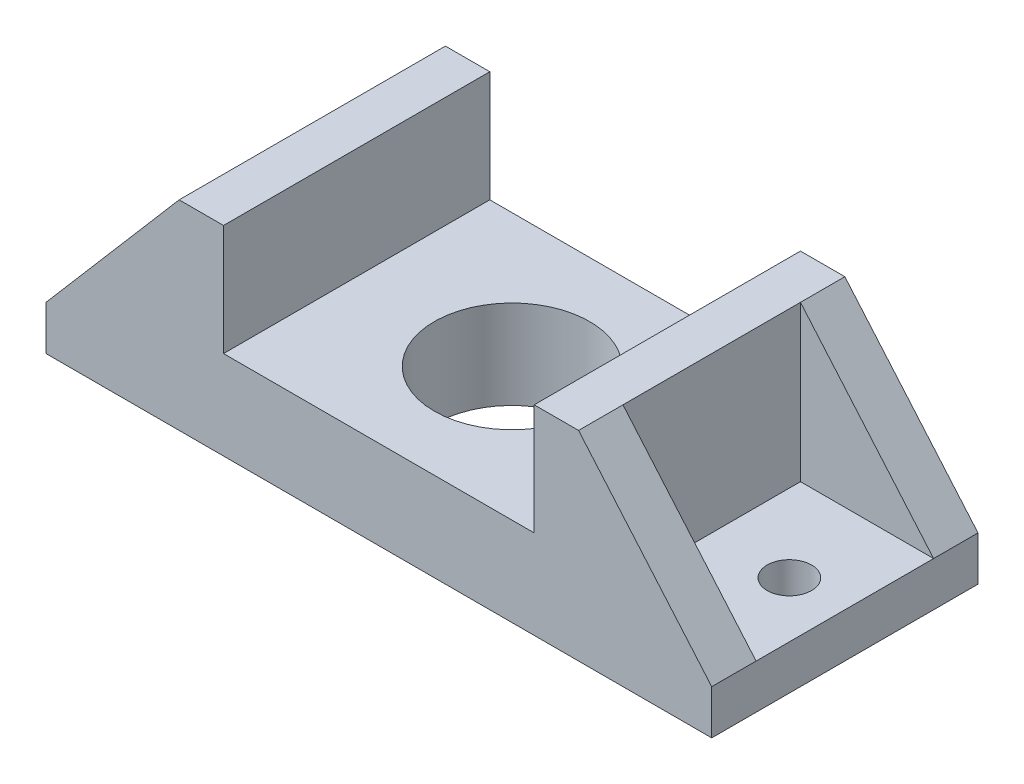
SolidWorks part; units mm, degrees
ref_plane "Ön Düzlem" through (0, 0, 0) normal (0, 0, 1) x (1, 0, 0)
ref_plane "Üst Düzlem" through (0, 0, 0) normal (0, 1, 0) x (1, 0, 0)
ref_plane "Sağ Düzlem" through (0, 0, 0) normal (1, 0, 0) x (0, 0, -1)
sketch "Çizim1" plane through (0, 0, 0) normal (0, 1, 0) x (1, 0, 0)
  line L1 (0, 0) -> (300, 0)
  line L2 (0, 0) -> (0, 120)
  line L3 (0, 120) -> (300, 120)
  line L4 (300, 0) -> (300, 120)
  dimension "D1" = 120
  dimension "D2" = 300
extrude "Yükseklik-Ekstrüzyon1" add sketch "Çizim1" along normal blind 20
sketch "Çizim2" plane through (0, 20, 0) normal (0, 1, 0) x (1, 0, 0)
  line L0 (300, 120) -> (0, 120) construction
  line L1 (60, 120) -> (80, 120)
  line L2 (60, 120) -> (60, 0)
  line L3 (60, 0) -> (80, 0)
  line L4 (80, 120) -> (80, 0)
  line L5 (0, 0) -> (300, 0) construction
  line L6 (0, 120) -> (0, 0) construction
  dimension "D1" = 20
  dimension "D2" = 60
extrude "Yükseklik-Ekstrüzyon2" add sketch "Çizim2" along normal blind 70
ref_plane "Düzlem1" through (150, 0, 0) normal (-1, 0, 0) x (0, 0, 1)
mirror "Aynalama1" about plane through (150, 0, 0) normal (-1, 0, 0) of "Yükseklik-Ekstrüzyon2"
sketch "Çizim3" plane through (0, 20, 0) normal (0, 1, 0) x (1, 0, 0)
  line L1 (80, 120) -> (220, 120)
  line L2 (80, 120) -> (80, 0)
  line L3 (80, 0) -> (220, 0)
  line L4 (220, 120) -> (220, 0)
extrude "Yükseklik-Ekstrüzyon3" add sketch "Çizim3" along normal blind 20
ref_plane "Düzlem2" through (0, 0, -60) normal (0, 0, 1) x (1, 0, 0)
sketch "Çizim4" plane through (0, 0, 0) normal (0, 0, 1) x (1, 0, 0)
  line L0 (0, 20) -> (60, 90)
  line L1 (60, 90) -> (60, 20)
  line L2 (60, 20) -> (0, 20)
extrude "Yükseklik-Ekstrüzyon4" add sketch "Çizim4" against normal blind 20
mirror "Aynalama2" about plane through (0, 0, -60) normal (0, 0, 1) of "Yükseklik-Ekstrüzyon4"
mirror "Aynalama3" about plane through (150, 0, 0) normal (-1, 0, 0) of "Aynalama2", "Yükseklik-Ekstrüzyon4"
sketch "Çizim5" plane through (0, 40, 0) normal (0, 1, 0) x (1, 0, 0)
  line L0 (0, 100) -> (0, 20) construction
  line L1 (220, 120) -> (80, 120) construction
  circle A0 centre (150, 60) radius 35
  dimension "D1" = 150
  dimension "D2" = 60
  dimension "D3" = 70
extrude "Kes-Ekstrüzyon1" cut sketch "Çizim5" against normal through all both and the other way through all
sketch "Çizim6" plane through (0, 20, 0) normal (0, 1, 0) x (1, 0, 0)
  line L0 (60, 120) -> (0, 120) construction
  line L1 (150, 120) -> (150, 54.9859) construction
  line L2 (220, 120) -> (80, 120) construction
  circle A0 centre (25, 60) radius 10
  circle A1 centre (150, 60) radius 35 construction
  circle A2 centre (275, 60) radius 10
  dimension "D1" = 20
  dimension "D2" = 125
  dimension "D3" = 60
extrude "Kes-Ekstrüzyon2" cut sketch "Çizim6" against normal blind 20
